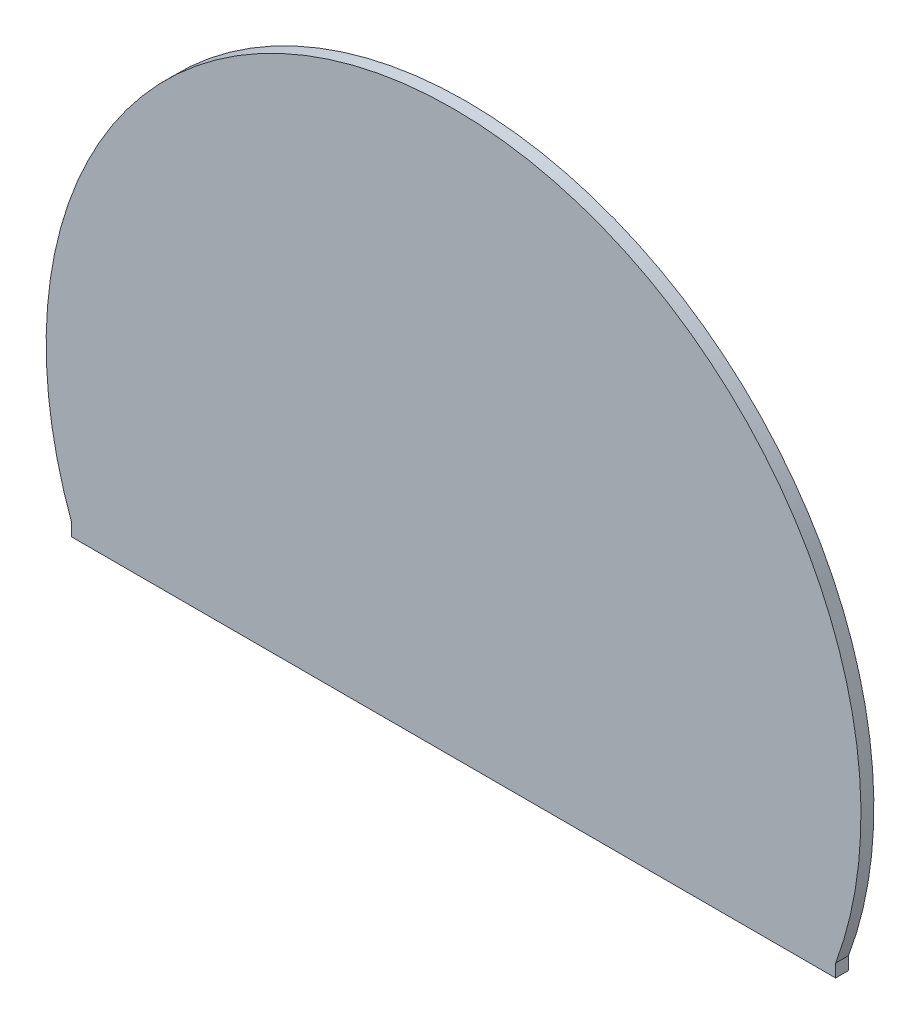
SolidWorks part; units mm, degrees
ref_plane "Front Plane" through (0, 0, 0) normal (0, 0, 1) x (1, 0, 0)
ref_plane "Top Plane" through (0, 0, 0) normal (0, 1, 0) x (1, 0, 0)
ref_plane "Right Plane" through (0, 0, 0) normal (1, 0, 0) x (0, 0, -1)
sketch "Sketch1" plane through (0, 0, 0) normal (0, 0, 1) x (1, 0, 0)
  line L0 (148.3381, -54.93) -> (148.3381, -59.93)
  line L1 (148.3381, -59.93) -> (-148.3381, -59.93)
  line L2 (-148.3381, -59.93) -> (-148.3381, -54.93)
  arc A1 (148.3381, -54.93) -> (-148.3381, -54.93) centre (0, 0) ccw
extrude "Boss-Extrude1" add sketch "Sketch1" along normal blind 5
